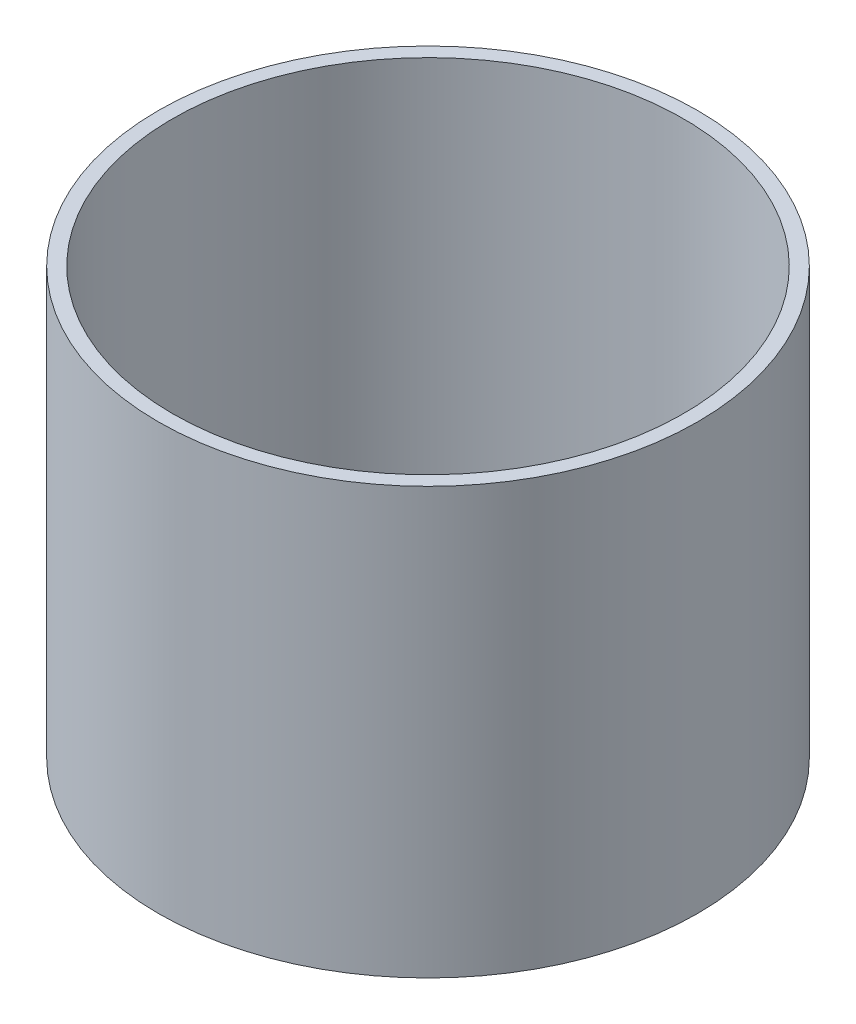
SolidWorks part; units mm, degrees
ref_plane "Front Plane" through (0, 0, 0) normal (0, 0, 1) x (1, 0, 0)
ref_plane "Top Plane" through (0, 0, 0) normal (0, 1, 0) x (1, 0, 0)
ref_plane "Right Plane" through (0, 0, 0) normal (1, 0, 0) x (0, 0, -1)
sketch "Sketch1" plane through (0, 0, 0) normal (0, 1, 0) x (1, 0, 0)
  circle A0 centre (0, 0) radius 90
  circle A1 centre (0, 0) radius 95
  dimension "D1" = 180
  dimension "D2" = 5
extrude "Boss-Extrude1" add sketch "Sketch1" along normal blind 150
